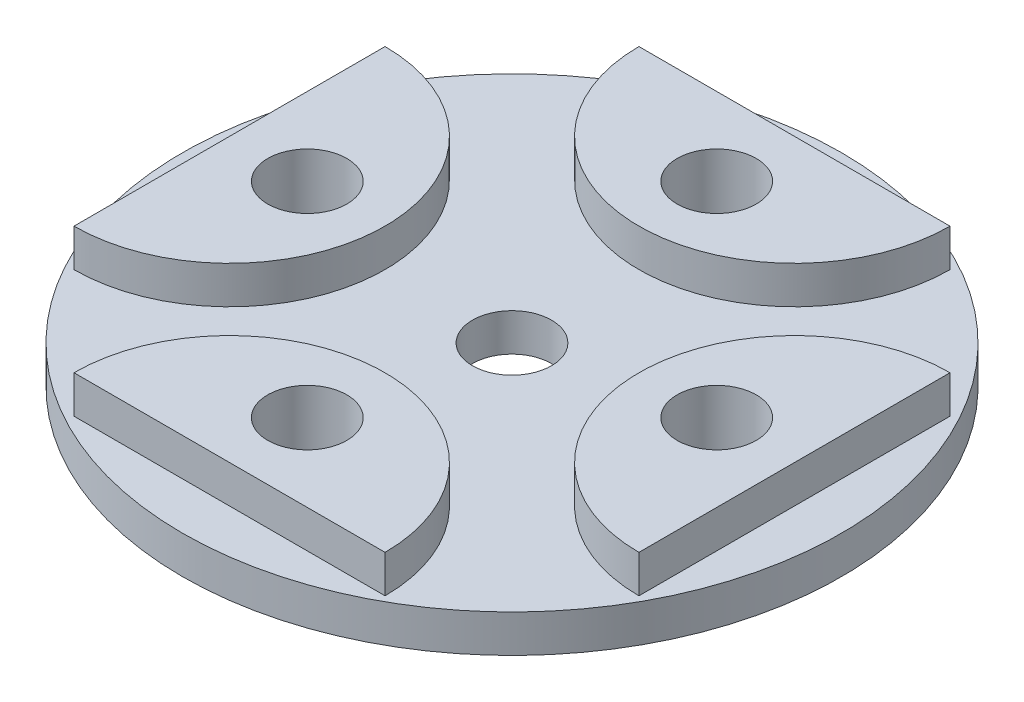
SolidWorks part; units mm, degrees
ref_plane "Front Plane" through (0, 0, 0) normal (0, 0, 1) x (1, 0, 0)
ref_plane "Top Plane" through (0, 0, 0) normal (0, 1, 0) x (1, 0, 0)
ref_plane "Right Plane" through (0, 0, 0) normal (1, 0, 0) x (0, 0, -1)
sketch "Sketch4" plane through (0, 0, 0) normal (0, 1, 0) x (1, 0, 0)
  circle A0 centre (0, 0) radius 17.5
  circle A1 centre (0, 0) radius 2.1
  dimension "D1" = 35
  dimension "D2" = 4.2
sketch "Sketch1" plane through (0, 0, 0) normal (0, 1, 0) x (1, 0, 0)
  line L0 (0, 0) -> (0, 15) construction
  line L1 (-8.26, 15) -> (8.26, 15)
  line L2 (15, 8.26) -> (15, -8.26)
  line L3 (8.26, -15) -> (-8.26, -15)
  line L4 (-15, -8.26) -> (-15, 8.26)
  arc A0 (-8.26, 15) -> (8.26, 15) centre (0, 15) ccw
  arc A1 (15, 8.26) -> (15, -8.26) centre (15, 0) ccw
  arc A2 (8.26, -15) -> (-8.26, -15) centre (0, -15) ccw
  arc A3 (-15, -8.26) -> (-15, 8.26) centre (-15, 0) ccw
  point P6 (8.26, 15)
  dimension "D2" = 16.52
  dimension "D1" = 15
  dimension "D3" = 4
extrude "Boss-Extrude1" add sketch "Sketch4" along normal blind 2
extrude "Boss-Extrude2" add sketch "Sketch1" along normal blind 4
sketch "Sketch5" plane through (0, 4, 0) normal (0, 1, 0) x (1, 0, 0)
  line L0 (0, 15) -> (0, 6.74) construction
  line L1 (8.26, 15) -> (-8.26, 15) construction
  line L2 (0, 0) -> (0, 8.77) construction
  arc A0 (-8.26, 15) -> (8.26, 15) centre (0, 15) ccw construction
  circle A1 centre (0, 10.87) radius 2.1
  circle A2 centre (10.87, 0) radius 2.1
  circle A3 centre (0, -10.87) radius 2.1
  circle A4 centre (-10.87, 0) radius 2.1
  dimension "D1" = 4.2
  dimension "D2" = 4
extrude "Cut-Extrude2" cut sketch "Sketch5" against normal through all
